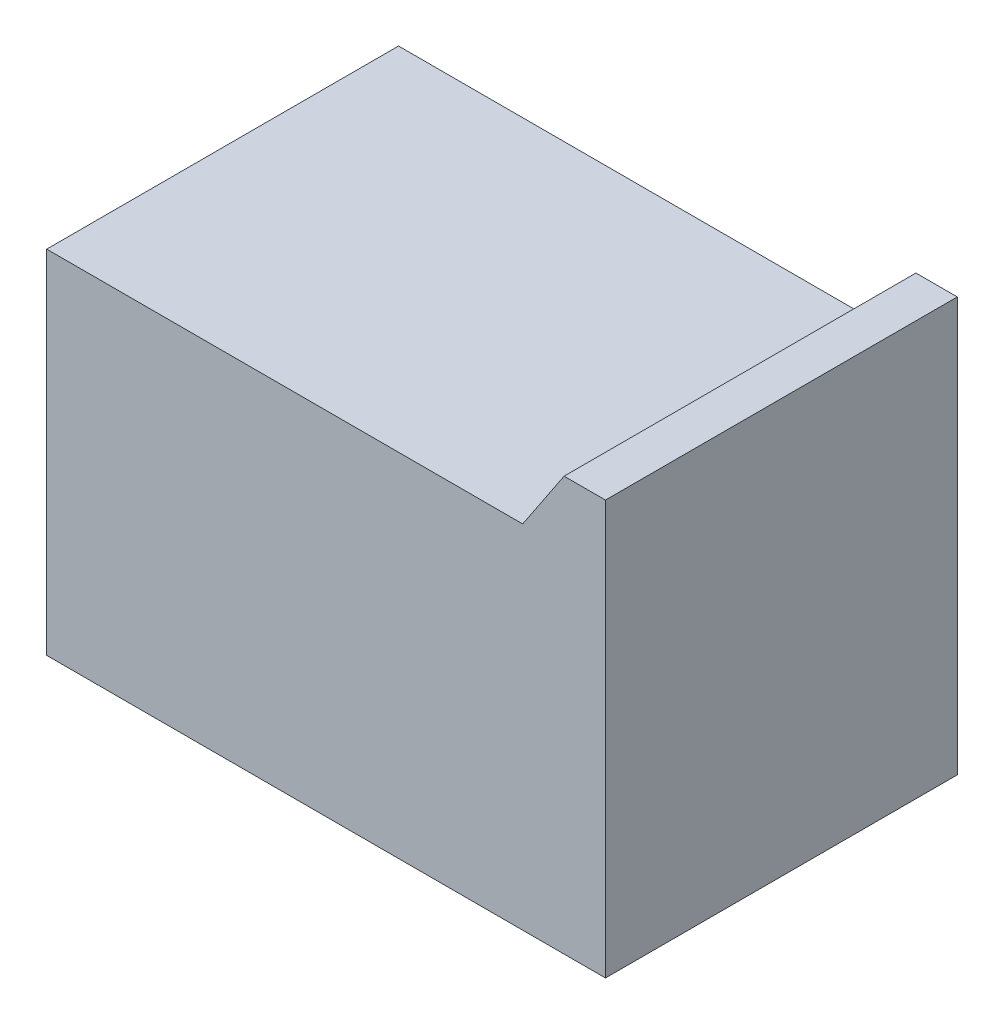
SolidWorks part; units mm, degrees
ref_plane "Front Plane" through (0, 0, 0) normal (0, 0, 1) x (1, 0, 0)
ref_plane "Top Plane" through (0, 0, 0) normal (0, 1, 0) x (1, 0, 0)
ref_plane "Right Plane" through (0, 0, 0) normal (1, 0, 0) x (0, 0, -1)
sketch "Sketch1" plane through (0, 0, 0) normal (0, 1, 0) x (1, 0, 0)
  line L1 (-342.9, -215.9) -> (342.9, -215.9)
  line L2 (-342.9, -215.9) -> (-342.9, 215.9)
  line L3 (-342.9, 215.9) -> (342.9, 215.9)
  line L4 (342.9, -215.9) -> (342.9, 215.9)
  line L5 (-342.9, -215.9) -> (342.9, 215.9) construction
  line L6 (-342.9, 215.9) -> (342.9, -215.9) construction
  point P0 (0, 0)
  dimension "D1" = 431.8
  dimension "D2" = 685.8
extrude "Boss-Extrude1" add sketch "Sketch1" along normal blind 508
sketch "Sketch2" plane through (0, 0, 215.9) normal (0, 0, 1) x (1, 0, 0)
  line L0 (-342.9, 431.8) -> (241.3, 431.8)
  line L1 (-342.9, 508) -> (-342.9, 0) construction
  line L2 (241.3, 431.8) -> (292.1, 508)
  line L3 (-342.9, 508) -> (342.9, 508) construction
  line L4 (-342.9, 431.8) -> (-342.9, 508)
  line L5 (-342.9, 508) -> (292.1, 508)
  dimension "D1" = 76.2
  dimension "D2" = 584.2
  dimension "D3" = 635
extrude "Cut-Extrude1" cut sketch "Sketch2" against normal through all
